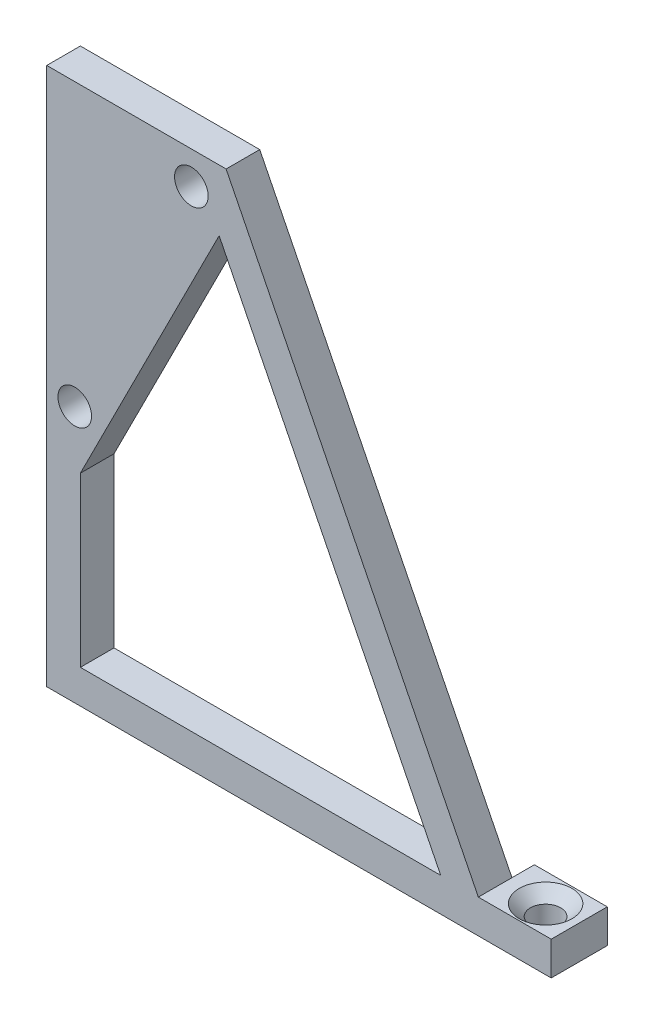
SolidWorks part; units mm, degrees
ref_plane "Přední rovina" through (0, 0, 0) normal (0, 0, 1) x (1, 0, 0)
ref_plane "Horní rovina" through (0, 0, 0) normal (0, 1, 0) x (1, 0, 0)
ref_plane "Pravá rovina" through (0, 0, 0) normal (1, 0, 0) x (0, 0, -1)
sketch "Skica1" plane through (0, 0, 0) normal (0, 0, 1) x (1, 0, 0)
  line L0 (0, 0) -> (40, 0)
  line L1 (40, 0) -> (45, 0)
  line L2 (45, 0) -> (45, 3)
  line L3 (45, 3) -> (38.5, 3)
  line L4 (38.5, 3) -> (16, 48)
  line L5 (16, 48) -> (0, 48)
  line L6 (0, 48) -> (0, 0)
  line L7 (3, 3) -> (35.1459, 3)
  line L8 (35.1459, 3) -> (15.3783, 42.5353)
  line L9 (15.3783, 42.5353) -> (3, 18)
  line L10 (3, 18) -> (3, 3)
  circle A0 centre (2.5, 22.9) radius 1.5
  circle A1 centre (12.9, 45.1) radius 1.5
  dimension "D12" = 3
  dimension "D13" = 3
  dimension "D1" = 40
  dimension "D2" = 5
  dimension "D3" = 3
  dimension "D4" = 6.5
  dimension "D5" = 16
  dimension "D6" = 48
  dimension "D7" = 3
  dimension "D8" = 15
  dimension "D9" = 3
  dimension "D10" = 5.5
  dimension "D11" = 3
  dimension "D14" = 12.9
  dimension "D15" = 2.9
  dimension "D16" = 2.5
  dimension "D17" = 25.1
extrude "Přidat vysunutím1" add sketch "Skica1" along normal blind 3
sketch "Skica3" plane through (0, 0, 0) normal (0, 0, -1) x (-1, 0, 0)
  line L0 (0, 0) -> (-45, 0) construction
  line L1 (-45, 3) -> (-38.5, 3)
  line L2 (-45, 3) -> (-45, 0)
  line L3 (-45, 0) -> (-38.5, 0)
  line L4 (-38.5, 3) -> (-38.5, 0)
  dimension "D1" = 6.5
extrude "Přidat vysunutím2" add sketch "Skica3" along normal blind 2
sketch "Skica4" plane through (0, 3, 0) normal (0, 1, 0) x (1, 0, 0)
  line L0 (38.5, 2) -> (45, 2) construction
  line L1 (45, -3) -> (45, 2) construction
  circle A0 centre (42, -0.5) radius 1.35
  dimension "D1" = 2.7
  dimension "D2" = 2.5
  dimension "D3" = 3
extrude "Odebrat vysunutím1" cut sketch "Skica4" against normal blind 3
chamfer "Zkosení1" distance 1 angle 45 1 edges at (40.65, 3, 0.5)
